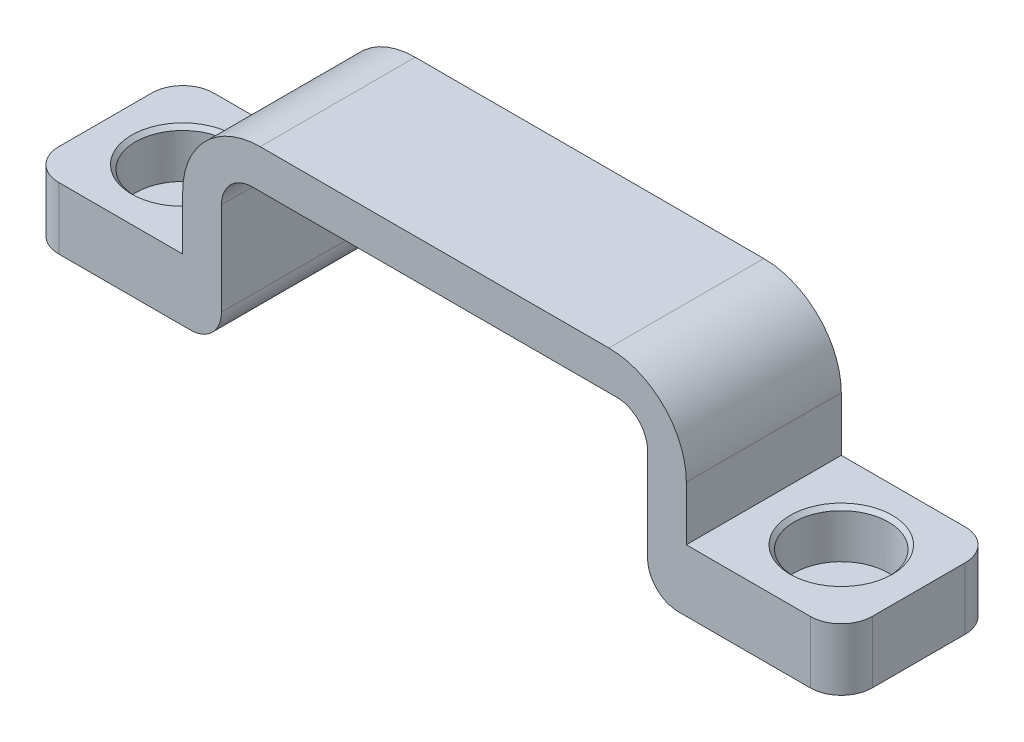
SolidWorks part; units mm, degrees
ref_plane "Front Plane" through (0, 0, 0) normal (0, 0, 1) x (1, 0, 0)
ref_plane "Top Plane" through (0, 0, 0) normal (0, 1, 0) x (1, 0, 0)
ref_plane "Right Plane" through (0, 0, 0) normal (1, 0, 0) x (0, 0, -1)
sketch "Sketch1" plane through (0, 0, 0) normal (0, 0, 1) x (1, 0, 0)
  line L0 (-16.25, 2.5) -> (16.25, 2.5)
  line L1 (16.25, 2.5) -> (16.25, -6)
  line L2 (16.25, -10) -> (13.75, -10)
  line L3 (13.75, -10) -> (13.75, 0)
  line L8 (0, 0) -> (0, 16.5989) construction
  line L9 (-13.75, 0) -> (13.75, 0)
  line L10 (16.25, -6) -> (26.25, -6)
  line L12 (16.25, -10) -> (26.25, -10)
  line L13 (26.25, -6) -> (26.25, -10)
  line L14 (21.25, -6) -> (21.25, -10) construction
  line L15 (-21.25, -6) -> (-21.25, -10) construction
  line L16 (-26.25, -6) -> (-26.25, -10)
  line L17 (-16.25, -10) -> (-26.25, -10)
  line L18 (-16.25, -6) -> (-26.25, -6)
  line L19 (-13.75, -10) -> (-13.75, 0)
  line L20 (-16.25, -10) -> (-13.75, -10)
  line L21 (-16.25, 2.5) -> (-16.25, -6)
  point P22 (0, 2.5)
  dimension "D5" = 2.5
  dimension "D6" = 4
  dimension "D7" = 10
  dimension "D1" = 2.5
  dimension "D2" = 42.5
  dimension "D3" = 10
extrude "Boss-Extrude1" add sketch "Sketch1" along normal mid plane 10
sketch "Sketch3" plane through (0, -6, 0) normal (0, 1, 0) x (1, 0, 0)
  line L0 (26.25, 0) -> (16.25, 0) construction
  line L1 (26.25, -5) -> (26.25, 5) construction
  line L2 (16.25, -5) -> (16.25, 5) construction
  line L3 (-26.25, 0) -> (-16.25, 0) construction
  line L4 (-26.25, -5) -> (-26.25, 5) construction
  line L5 (-16.25, -5) -> (-16.25, 5) construction
  circle A0 centre (21.25, 0) radius 3.05
  circle A1 centre (-21.25, 0) radius 3.05
  point P12 (-21.25, 0)
  point P13 (21.25, 0)
  dimension "D1" = 6.1
fillet "Fillet1" radius 2 2 edges at (13.75, 0, 0) (-13.75, 0, 0)
fillet "Fillet2" radius 5 2 edges at (-16.25, 2.5, 0) (16.25, 2.5, 0)
fillet "Fillet3" radius 2 4 edges at (-26.25, -8, -5) (-26.25, -8, 5) (26.25, -8, -5) (26.25, -8, 5)
fillet "Fillet4" radius 2 2 edges at (-13.75, -10, 0) (13.75, -10, 0)
extrude "Cut-Extrude1" cut sketch "Sketch3" against normal blind 3.1
chamfer "Chamfer1" distance 0.25 angle 45 2 edges at (-24.3, -6, 0) (18.2, -6, 0)
equation "\"D1@Sketch1\"=\"D5@Sketch1\""
